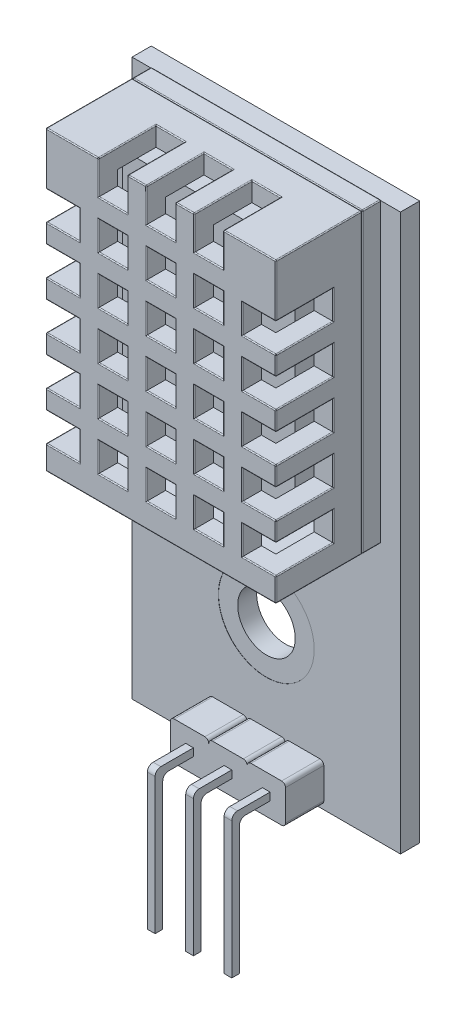
SolidWorks part; units mm, degrees
ref_plane "Front Plane" through (0, 0, 0) normal (0, 0, 1) x (1, 0, 0)
ref_plane "Top Plane" through (0, 0, 0) normal (0, 1, 0) x (1, 0, 0)
ref_plane "Right Plane" through (0, 0, 0) normal (1, 0, 0) x (0, 0, -1)
sketch "Sketch1" plane through (0, 0, 0) normal (0, 0, 1) x (1, 0, 0)
  line L1 (0, 0) -> (12, 0)
  line L2 (0, 0) -> (0, 15.5)
  line L3 (0, 15.5) -> (12, 15.5)
  line L4 (12, 0) -> (12, 15.5)
  dimension "D1" = 12
  dimension "D2" = 15.5
extrude "Boss-Extrude1" add sketch "Sketch1" along normal blind 5.5
shell "Shell2" thickness 1
sketch "Sketch3" plane through (0, 0, 5.5) normal (0, 0, 1) x (1, 0, 0)
  line L0 (12, 15.5) -> (0, 15.5) construction
  line L1 (2.75, 15.5) -> (4.25, 15.5)
  line L2 (2.75, 15.5) -> (2.75, 13.75)
  line L3 (2.75, 13.75) -> (4.25, 13.75)
  line L4 (4.25, 15.5) -> (4.25, 13.75)
  line L5 (5.25, 15.5) -> (6.75, 15.5)
  line L6 (5.25, 15.5) -> (5.25, 13.75)
  line L7 (5.25, 13.75) -> (6.75, 13.75)
  line L8 (6.75, 15.5) -> (6.75, 13.75)
  line L9 (7.75, 15.5) -> (9.25, 15.5)
  line L10 (7.75, 15.5) -> (7.75, 13.75)
  line L11 (7.75, 13.75) -> (9.25, 13.75)
  line L12 (9.25, 15.5) -> (9.25, 13.75)
  line L13 (0, 15.5) -> (0, 0) construction
  dimension "D1" = 1.5
  dimension "D2" = 1.75
  dimension "D4" = 2.75
  dimension "D3" = 3
extrude "Cut-Extrude1" cut sketch "Sketch3" against normal blind 3
sketch "Sketch4" plane through (0, 0, 5.5) normal (0, 0, 1) x (1, 0, 0)
  line L0 (2.75, 13.75) -> (4.25, 13.75) construction
  line L1 (2.75, 12.75) -> (4.25, 12.75)
  line L2 (2.75, 12.75) -> (2.75, 11.25)
  line L3 (2.75, 11.25) -> (4.25, 11.25)
  line L4 (4.25, 12.75) -> (4.25, 11.25)
  line L5 (0, 15.5) -> (0, 0) construction
  line L6 (5.25, 12.75) -> (6.75, 12.75)
  line L7 (5.25, 12.75) -> (5.25, 11.25)
  line L8 (5.25, 11.25) -> (6.75, 11.25)
  line L9 (6.75, 12.75) -> (6.75, 11.25)
  line L10 (7.75, 12.75) -> (9.25, 12.75)
  line L11 (7.75, 12.75) -> (7.75, 11.25)
  line L12 (7.75, 11.25) -> (9.25, 11.25)
  line L13 (9.25, 12.75) -> (9.25, 11.25)
  line L14 (5.25, 10.25) -> (6.75, 10.25)
  line L15 (5.25, 10.25) -> (5.25, 8.75)
  line L16 (5.25, 8.75) -> (6.75, 8.75)
  line L17 (6.75, 10.25) -> (6.75, 8.75)
  line L18 (7.75, 10.25) -> (9.25, 10.25)
  line L19 (7.75, 10.25) -> (7.75, 8.75)
  line L20 (7.75, 8.75) -> (9.25, 8.75)
  line L21 (9.25, 10.25) -> (9.25, 8.75)
  line L22 (5.25, 7.75) -> (6.75, 7.75)
  line L23 (5.25, 7.75) -> (5.25, 6.25)
  line L24 (5.25, 6.25) -> (6.75, 6.25)
  line L25 (6.75, 7.75) -> (6.75, 6.25)
  line L26 (7.75, 7.75) -> (9.25, 7.75)
  line L27 (7.75, 7.75) -> (7.75, 6.25)
  line L28 (7.75, 6.25) -> (9.25, 6.25)
  line L29 (9.25, 7.75) -> (9.25, 6.25)
  line L30 (5.25, 5.25) -> (6.75, 5.25)
  line L31 (5.25, 5.25) -> (5.25, 3.75)
  line L32 (5.25, 3.75) -> (6.75, 3.75)
  line L33 (6.75, 5.25) -> (6.75, 3.75)
  line L34 (7.75, 5.25) -> (9.25, 5.25)
  line L35 (7.75, 5.25) -> (7.75, 3.75)
  line L36 (7.75, 3.75) -> (9.25, 3.75)
  line L37 (9.25, 5.25) -> (9.25, 3.75)
  line L38 (5.25, 2.75) -> (6.75, 2.75)
  line L39 (5.25, 2.75) -> (5.25, 1.25)
  line L40 (5.25, 1.25) -> (6.75, 1.25)
  line L41 (6.75, 2.75) -> (6.75, 1.25)
  line L42 (7.75, 2.75) -> (9.25, 2.75)
  line L43 (7.75, 2.75) -> (7.75, 1.25)
  line L44 (7.75, 1.25) -> (9.25, 1.25)
  line L45 (9.25, 2.75) -> (9.25, 1.25)
  line L46 (2.75, 10.25) -> (4.25, 10.25)
  line L47 (2.75, 10.25) -> (2.75, 8.75)
  line L48 (2.75, 8.75) -> (4.25, 8.75)
  line L49 (4.25, 10.25) -> (4.25, 8.75)
  line L50 (2.75, 7.75) -> (4.25, 7.75)
  line L51 (2.75, 7.75) -> (2.75, 6.25)
  line L52 (2.75, 6.25) -> (4.25, 6.25)
  line L53 (4.25, 7.75) -> (4.25, 6.25)
  line L54 (2.75, 5.25) -> (4.25, 5.25)
  line L55 (2.75, 5.25) -> (2.75, 3.75)
  line L56 (2.75, 3.75) -> (4.25, 3.75)
  line L57 (4.25, 5.25) -> (4.25, 3.75)
  line L58 (2.75, 2.75) -> (4.25, 2.75)
  line L59 (2.75, 2.75) -> (2.75, 1.25)
  line L60 (2.75, 1.25) -> (4.25, 1.25)
  line L61 (4.25, 2.75) -> (4.25, 1.25)
  dimension "D1" = 1.5
  dimension "D2" = 1
  dimension "D3" = 2.75
  dimension "D4" = 3
  dimension "D5" = 5
extrude "Cut-Extrude2" cut sketch "Sketch4" against normal blind 3
sketch "Sketch5" plane through (0, 0, 5.5) normal (0, 0, 1) x (1, 0, 0)
  line L0 (0, 15.5) -> (0, 0) construction
  line L1 (0, 12.75) -> (1.75, 12.75)
  line L2 (0, 12.75) -> (0, 11.25)
  line L3 (0, 11.25) -> (1.75, 11.25)
  line L4 (1.75, 12.75) -> (1.75, 11.25)
  line L7 (2.75, 12.75) -> (2.75, 11.25) construction
  line L8 (10.25, 12.75) -> (12, 12.75)
  line L9 (10.25, 12.75) -> (10.25, 11.25)
  line L10 (10.25, 11.25) -> (12, 11.25)
  line L11 (12, 12.75) -> (12, 11.25)
  line L12 (10.25, 10.25) -> (12, 10.25)
  line L13 (10.25, 10.25) -> (10.25, 8.75)
  line L14 (10.25, 8.75) -> (12, 8.75)
  line L15 (12, 10.25) -> (12, 8.75)
  line L16 (10.25, 7.75) -> (12, 7.75)
  line L17 (10.25, 7.75) -> (10.25, 6.25)
  line L18 (10.25, 6.25) -> (12, 6.25)
  line L19 (12, 7.75) -> (12, 6.25)
  line L20 (10.25, 5.25) -> (12, 5.25)
  line L21 (10.25, 5.25) -> (10.25, 3.75)
  line L22 (10.25, 3.75) -> (12, 3.75)
  line L23 (12, 5.25) -> (12, 3.75)
  line L24 (10.25, 2.75) -> (12, 2.75)
  line L25 (10.25, 2.75) -> (10.25, 1.25)
  line L26 (10.25, 1.25) -> (12, 1.25)
  line L27 (12, 2.75) -> (12, 1.25)
  line L28 (0, 10.25) -> (1.75, 10.25)
  line L29 (0, 10.25) -> (0, 8.75)
  line L30 (0, 8.75) -> (1.75, 8.75)
  line L31 (1.75, 10.25) -> (1.75, 8.75)
  line L32 (0, 7.75) -> (1.75, 7.75)
  line L33 (0, 7.75) -> (0, 6.25)
  line L34 (0, 6.25) -> (1.75, 6.25)
  line L35 (1.75, 7.75) -> (1.75, 6.25)
  line L36 (0, 5.25) -> (1.75, 5.25)
  line L37 (0, 5.25) -> (0, 3.75)
  line L38 (0, 3.75) -> (1.75, 3.75)
  line L39 (1.75, 5.25) -> (1.75, 3.75)
  line L40 (0, 2.75) -> (1.75, 2.75)
  line L41 (0, 2.75) -> (0, 1.25)
  line L42 (0, 1.25) -> (1.75, 1.25)
  line L43 (1.75, 2.75) -> (1.75, 1.25)
  dimension "D1" = 1
  dimension "D2" = 2
  dimension "D3" = 5
extrude "Cut-Extrude3" cut sketch "Sketch5" against normal blind 3
sketch "Sketch6" plane through (0, 0, 0) normal (0, 0, -1) x (-1, 0, 0)
  line L4 (0, 0) -> (0, 15.5)
  line L5 (0, 15.5) -> (-12, 15.5)
  line L6 (-12, 15.5) -> (-12, 0)
  line L7 (-12, 0) -> (0, 0)
  line L8 (0, 0) -> (0, 15.5)
  line L9 (0, 15.5) -> (-12, 15.5)
  line L10 (-12, 15.5) -> (-12, 0)
  line L11 (-12, 0) -> (0, 0)
  line L12 (-1, 14.5) -> (-11, 14.5)
  line L13 (-1, 1) -> (-1, 14.5)
  line L14 (-11, 1) -> (-1, 1)
  line L15 (-11, 14.5) -> (-11, 1)
  line L16 (-1, 14.5) -> (-11, 14.5)
  line L17 (-1, 1) -> (-1, 14.5)
  line L18 (-11, 1) -> (-1, 1)
  line L19 (-11, 14.5) -> (-11, 1)
  dimension "D1" = 0
  dimension "D2" = 0
extrude "Cut-Extrude4" cut sketch "Sketch6" against normal blind 1
ref_plane "Plane1" through (0, 0, 0.99) normal (0, 0, 1) x (1, 0, 0)
sketch "Sketch8" plane through (0, 0, 0.99) normal (0, 0, 1) x (1, 0, 0)
  line L4 (0, 0) -> (12, 0)
  line L5 (0, 15.5) -> (0, 0)
  line L6 (12, 15.5) -> (0, 15.5)
  line L7 (12, 0) -> (12, 15.5)
  line L8 (0, 0) -> (12, 0)
  line L9 (0, 15.5) -> (0, 0)
  line L10 (12, 15.5) -> (0, 15.5)
  line L11 (12, 0) -> (12, 15.5)
  dimension "D1" = 0
extrude "Boss-Extrude3" add sketch "Sketch8" against normal blind 0.99 separate body
fillet "Fillet1" radius 0.05 106 edges at (0, 12.75, 4) (0, 12, 2.5) (0, 11.25, 4) (0, 10.25, 4) (0, 9.5, 2.5) (0, 8.75, 4) (0, 6.25, 4) (0, 4.5, 2.5) (0, 2.75, 4) (0, 2, 2.5) (0, 1.25, 4) (0, 7.75, 1) (9.25, 15.5, 4) (8.5, 15.5, 2.5) (6.75, 15.5, 4) (6, 15.5, 2.5) (5.25, 15.5, 4) (2.75, 15.5, 4) (0, 15.5, 3.25) (12, 0, 3.25) (12, 1.25, 4) (12, 4.5, 2.5) (12, 5.25, 4) (12, 7, 2.5) (12, 9.5, 2.5) (12, 10.25, 4) (12, 11.25, 4) (12, 12, 2.5) (12, 15.5, 3.25) (0.875, 3.75, 5.5) (0, 5.75, 5.5) (0.875, 6.25, 5.5) (0.875, 7.75, 5.5) (0, 8.25, 5.5) (0.875, 11.25, 5.5) (1.75, 12, 5.5) (0.875, 12.75, 5.5) (0, 14.125, 5.5) (1.375, 15.5, 5.5) (2.75, 14.625, 5.5) (3.5, 13.75, 5.5) (5.25, 14.625, 5.5) (6, 13.75, 5.5) (7.25, 15.5, 5.5) (8.5, 13.75, 5.5) (9.25, 14.625, 5.5) (12, 14.125, 5.5) (11.125, 12.75, 5.5) (11.125, 11.25, 5.5) (12, 10.75, 5.5) (11.125, 8.75, 5.5) (12, 8.25, 5.5) (11.125, 7.75, 5.5) (10.25, 7, 5.5) (11.125, 5.25, 5.5) (10.25, 4.5, 5.5) (11.125, 3.75, 5.5) (12, 3.25, 5.5) (11.125, 2.75, 5.5) (11.125, 1.25, 5.5) (6, 0, 5.5) (0.875, 1.25, 5.5) (0, 3.25, 5.5) (4.25, 12, 5.5) (3.5, 12.75, 5.5) (2.75, 12, 5.5) (3.5, 11.25, 5.5) (6.75, 12, 5.5) (6, 12.75, 5.5) (9.25, 12, 5.5) (8.5, 12.75, 5.5) (7.75, 12, 5.5) (8.5, 11.25, 5.5) (6.75, 9.5, 5.5) (6, 10.25, 5.5) (5.25, 9.5, 5.5) (6, 8.75, 5.5) (8.5, 10.25, 5.5) (7.75, 9.5, 5.5) (6, 7.75, 5.5) (5.25, 7, 5.5) (6, 6.25, 5.5) (7.75, 7, 5.5) (8.5, 6.25, 5.5) (8.5, 5.25, 5.5) (7.75, 4.5, 5.5) (8.5, 3.75, 5.5) (6.75, 2, 5.5) (6, 2.75, 5.5) (5.25, 2, 5.5) (6, 1.25, 5.5) (9.25, 2, 5.5) (8.5, 2.75, 5.5) (7.75, 2, 5.5) (8.5, 1.25, 5.5) (4.25, 9.5, 5.5) (3.5, 10.25, 5.5) (2.75, 9.5, 5.5) (3.5, 8.75, 5.5) (4.25, 7, 5.5) (3.5, 7.75, 5.5) (2.75, 7, 5.5) (4.25, 4.5, 5.5) (3.5, 5.25, 5.5) (4.25, 2, 5.5) (2.75, 2, 5.5)
fillet "Fillet2" radius 0.05 12 edges at (6, 15.5, 0.99) (0, 15.5, 0.495) (0, 7.75, 0.99) (0, 0, 0.495) (6, 0, 0.99) (12, 15.5, 0.495) (12, 0, 0.495) (12, 7.75, 0.99) (6, 15.5, 0) (0, 7.75, 0) (6, 0, 0) (12, 7.75, 0)
sketch "Sketch10" plane through (0, 0, 0.99) normal (0, 0, 1) x (1, 0, 0)
  line L14 (1.5, 1.5) -> (10.5, 1.5)
  line L15 (10.5, 1.5) -> (10.5, 14)
  line L16 (10.5, 14) -> (1.5, 14)
  line L17 (1.5, 14) -> (1.5, 1.5)
  line L18 (1.5, 1.5) -> (10.5, 1.5)
  line L19 (10.5, 1.5) -> (10.5, 14)
  line L20 (10.5, 14) -> (1.5, 14)
  line L21 (1.5, 14) -> (1.5, 1.5)
  dimension "D1" = 0.5
extrude "Boss-Extrude4" add sketch "Sketch10" along normal blind 2
sketch "Sketch11" plane through (0, 0, 0) normal (0, 0, -1) x (-1, 0, 0)
  line L0 (-11.95, 0.05) -> (-0.05, 0.05) construction
  line L1 (-13, 15.45) -> (1, 15.45)
  line L2 (-13, 15.45) -> (-13, -13.55)
  line L3 (-13, -13.55) -> (1, -13.55)
  line L4 (1, 15.45) -> (1, -13.55)
  point P4 (-6, 15.45)
  point P7 (-6, 0.05)
  dimension "D1" = 14
  dimension "D2" = 29
  dimension "D3" = 0
  dimension "D4" = 14
extrude "Boss-Extrude5" add sketch "Sketch11" along normal blind 1
sketch "Sketch12" plane through (0, 0, 0) normal (0, 0, 1) x (1, 0, 0)
  line L2 (3, -11.55) -> (3, -13.15)
  line L4 (9, -11.55) -> (9, -13.15)
  line L5 (13, 15.45) -> (13, -13.55) construction
  line L7 (5, -11.55) -> (5, -13.15)
  line L8 (7, -11.55) -> (7, -13.15)
  line L9 (3.2, -11.35) -> (4.8, -11.35)
  line L10 (6.8, -11.35) -> (5.2, -11.35)
  line L11 (8.8, -11.35) -> (7.2, -11.35)
  line L12 (9, -13.35) -> (9, -11.35)
  line L13 (8.8, -13.35) -> (7.2, -13.35)
  line L14 (6.8, -13.35) -> (5.2, -13.35)
  line L15 (4.8, -13.35) -> (3.2, -13.35)
  arc A0 (3, -11.55) -> (3.2, -11.35) centre (3.2, -11.55) cw
  arc A1 (5, -11.55) -> (4.8, -11.35) centre (4.8, -11.55) ccw
  arc A2 (5, -11.55) -> (5.2, -11.35) centre (5.2, -11.55) cw
  arc A3 (3.2, -13.35) -> (3, -13.15) centre (3.2, -13.15) cw
  arc A4 (4.8, -13.35) -> (5, -13.15) centre (4.8, -13.15) ccw
  arc A5 (5, -13.15) -> (5.2, -13.35) centre (5.2, -13.15) ccw
  arc A6 (7, -13.15) -> (6.8, -13.35) centre (6.8, -13.15) cw
  arc A7 (7, -13.15) -> (7.2, -13.35) centre (7.2, -13.15) ccw
  arc A8 (7, -11.55) -> (6.8, -11.35) centre (6.8, -11.55) ccw
  arc A9 (7, -11.55) -> (7.2, -11.35) centre (7.2, -11.55) cw
  arc A10 (9, -11.55) -> (8.8, -11.35) centre (8.8, -11.55) ccw
  arc A11 (9, -13.15) -> (8.8, -13.35) centre (8.8, -13.15) cw
  point P8 (3, -11.35)
  dimension "D3" = 0.2
  dimension "D5" = 0.2
  dimension "D6" = 0.2
  dimension "D8" = 0.2
  dimension "D9" = 0.2
  dimension "D10" = 0.2
  dimension "D11" = 0.2
  dimension "D12" = 0.2
  dimension "D13" = 0.2
  dimension "D14" = 0.2
  dimension "D15" = 0.2
  dimension "D16" = 0.2
  dimension "D1" = 6
  dimension "D2" = 2
  dimension "D4" = 4
  dimension "D7" = 2
extrude "Boss-Extrude6" add sketch "Sketch12" along normal blind 2 contours L15 A4 L7 A1 L9 A0 L2 A3 | L8 A8 L10 A2 L7 A5 L14 A6 | A11 L4 A10 L11 A9 L8 A7 L13
sketch "Sketch13" plane through (0, 0, 2) normal (0, 0, 1) x (1, 0, 0)
  line L0 (3.2, -11.35) -> (4.8, -11.35) construction
  line L1 (3.8, -12.1506) -> (4.2, -12.1506)
  line L2 (3.8, -12.1506) -> (3.8, -12.5494)
  line L3 (3.8, -12.5494) -> (4.2, -12.5494)
  line L4 (4.2, -12.1506) -> (4.2, -12.5494)
  line L5 (3, -11.55) -> (3, -13.15) construction
  line L6 (6.8, -11.35) -> (5.2, -11.35) construction
  line L7 (5.8, -12.1506) -> (6.2, -12.1506)
  line L8 (5.8, -12.1506) -> (5.8, -12.5494)
  line L9 (5.8, -12.5494) -> (6.2, -12.5494)
  line L10 (6.2, -12.1506) -> (6.2, -12.5494)
  line L11 (8.8, -11.35) -> (7.2, -11.35) construction
  line L12 (7.8, -12.1506) -> (8.2, -12.1506)
  line L13 (7.8, -12.1506) -> (7.8, -12.5494)
  line L14 (7.8, -12.5494) -> (8.2, -12.5494)
  line L15 (8.2, -12.1506) -> (8.2, -12.5494)
  point P4 (4, -12.1506)
  point P7 (4, -11.35)
  point P8 (3.8, -12.35)
  point P11 (3, -12.35)
  point P16 (6, -12.1506)
  point P19 (6, -11.35)
  point P24 (8, -12.1506)
  point P27 (8, -11.35)
  dimension "D1" = 0.4
  dimension "D2" = 0.3988
  dimension "D3" = 0
  dimension "D4" = 0
  dimension "D5" = 0.4
  dimension "D6" = 0
  dimension "D7" = 0.4
  dimension "D8" = 0
extrude "Boss-Extrude7" add sketch "Sketch13" along normal blind 2
sketch "Sketch14" plane through (0, -12.5494, 0) normal (0, -1, 0) x (1, 0, 0)
  line L0 (6.2, 4) -> (6.2, 2) construction
  line L1 (5.8, 4) -> (6.2, 4)
  line L2 (5.8, 4) -> (5.8, 3.5997)
  line L3 (5.8, 3.5997) -> (6.2, 3.5997)
  line L4 (6.2, 4) -> (6.2, 3.5997)
  line L5 (4.2, 4) -> (4.2, 2) construction
  line L6 (3.8, 4) -> (4.2, 4)
  line L7 (3.8, 4) -> (3.8, 3.5997)
  line L8 (3.8, 3.5997) -> (4.2, 3.5997)
  line L9 (4.2, 4) -> (4.2, 3.5997)
  line L10 (8.2, 4) -> (8.2, 2) construction
  line L11 (7.8, 4) -> (8.2, 4)
  line L12 (7.8, 4) -> (7.8, 3.5997)
  line L13 (7.8, 3.5997) -> (8.2, 3.5997)
  line L14 (8.2, 4) -> (8.2, 3.5997)
extrude "Boss-Extrude8" add sketch "Sketch14" along normal blind 7
fillet "Fillet3" radius 0.3 1 edges at (4, -12.5494, 3.5997)
fillet "Fillet4" radius 0.3 1 edges at (6, -12.5494, 3.5997)
fillet "Fillet5" radius 0.3 1 edges at (8, -12.5494, 3.5997)
fillet "Fillet6" radius 0.3 1 edges at (4, -12.1506, 4)
fillet "Fillet7" radius 0.3 1 edges at (6, -12.1506, 4)
fillet "Fillet8" radius 0.3 1 edges at (8, -12.1506, 4)
sketch "Sketch15" plane through (0, 0, 0) normal (0, 0, 1) x (1, 0, 0)
  circle A0 centre (6, -6.5668) radius 1.5
  dimension "D1" = 3
extrude "Cut-Extrude5" cut sketch "Sketch15" against normal through all
sketch "Sketch16" plane through (0, 0, 0) normal (0, 0, 1) x (1, 0, 0)
  circle A0 centre (6, -6.5668) radius 2.5
  dimension "D1" = 5
extrude "Cut-Extrude6" cut sketch "Sketch16" against normal blind 0.01
